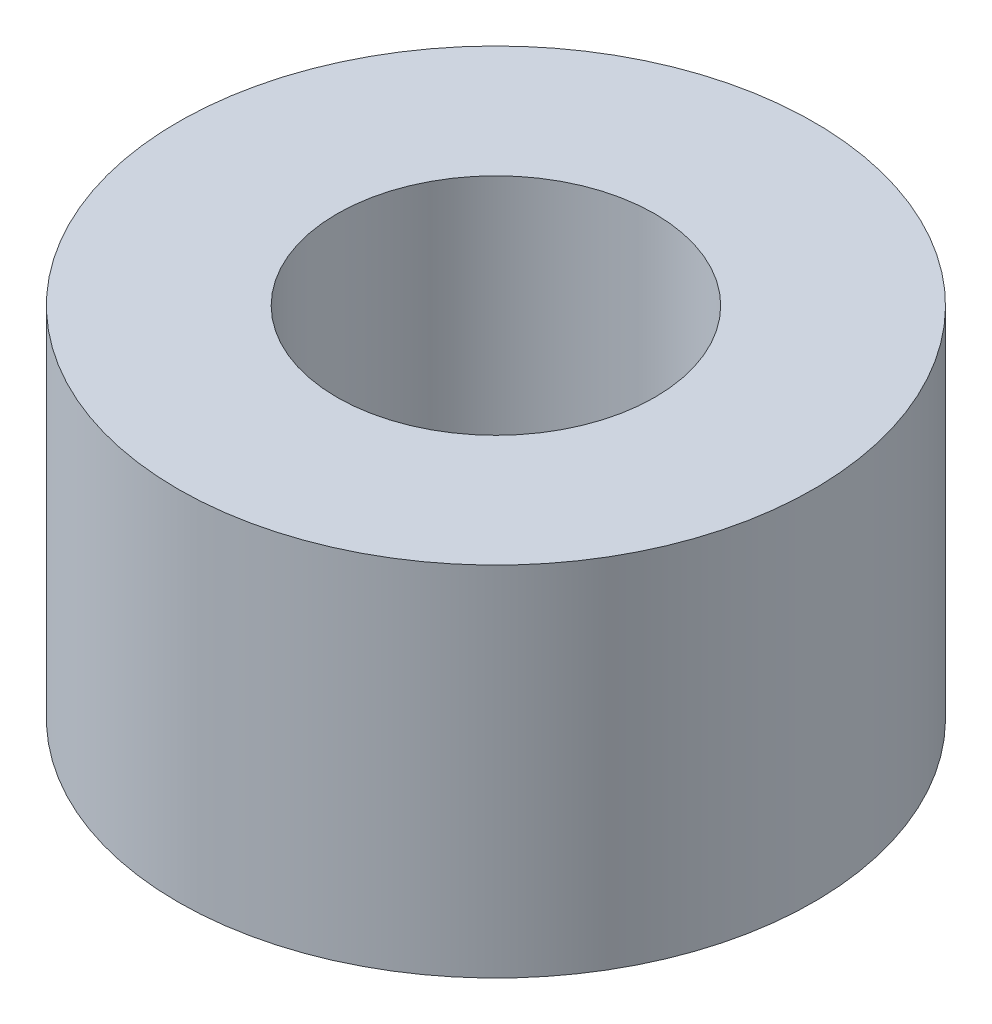
SolidWorks part; units mm, degrees
ref_plane "Front Plane" through (0, 0, 0) normal (0, 0, 1) x (1, 0, 0)
ref_plane "Top Plane" through (0, 0, 0) normal (0, 1, 0) x (1, 0, 0)
ref_plane "Right Plane" through (0, 0, 0) normal (1, 0, 0) x (0, 0, -1)
sketch "Sketch1" plane through (0, 0, 0) normal (0, 1, 0) x (1, 0, 0)
  circle A0 centre (0, 0) radius 2
  circle A1 centre (0, 0) radius 4
  dimension "D1" = 4
  dimension "D2" = 8
extrude "Boss-Extrude1" add sketch "Sketch1" along normal blind 4.5
